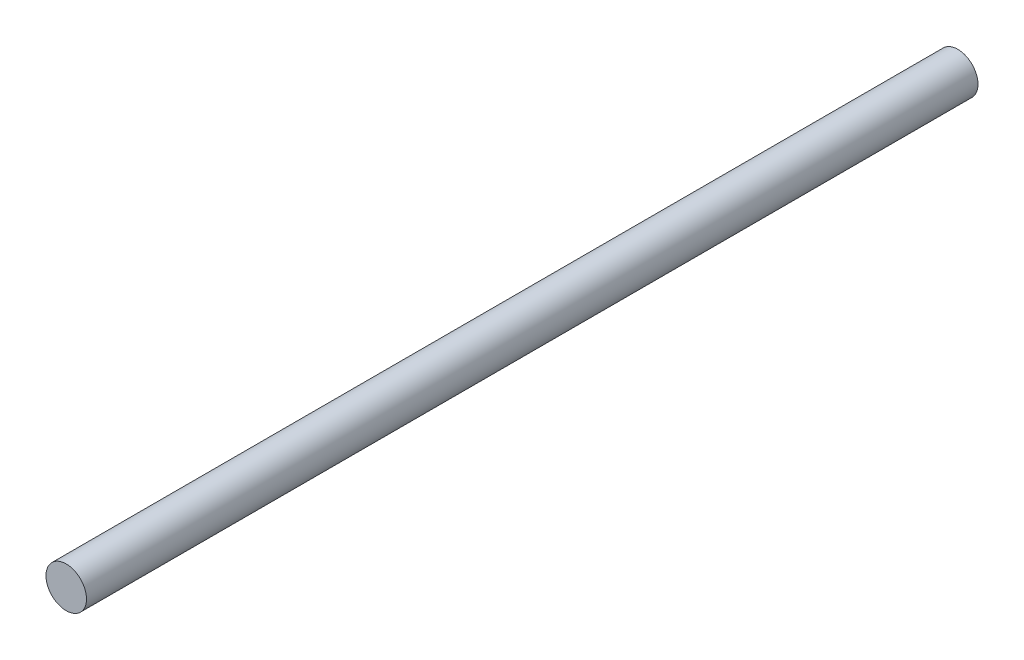
SolidWorks part; units mm, degrees
ref_plane "Plano frontal" through (0, 0, 0) normal (0, 0, 1) x (1, 0, 0)
ref_plane "Plano superior" through (0, 0, 0) normal (0, 1, 0) x (1, 0, 0)
ref_plane "Plano direito" through (0, 0, 0) normal (1, 0, 0) x (0, 0, -1)
sketch "Esboço1" plane through (0, 0, 0) normal (0, 0, 1) x (1, 0, 0)
  circle A0 centre (0, 0) radius 4
extrude "Ressalto-extrusão1" add sketch "Esboço1" along normal blind 176
